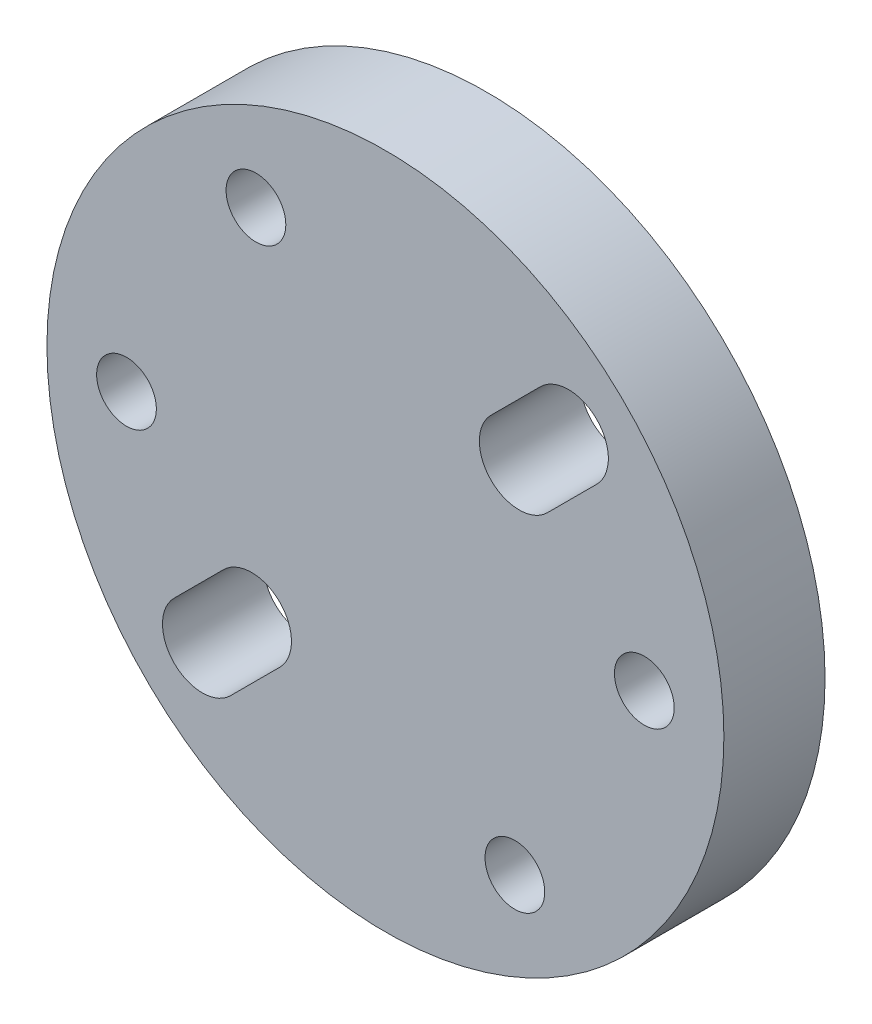
SolidWorks part; units mm, degrees
material "6061-T6 (SS)"
ref_plane "Front Plane" through (0, 0, 0) normal (0, 0, 1) x (1, 0, 0)
ref_plane "Top Plane" through (0, 0, 0) normal (0, 1, 0) x (1, 0, 0)
ref_plane "Right Plane" through (0, 0, 0) normal (1, 0, 0) x (0, 0, -1)
sketch "Sketch1" plane through (0, 0, 0) normal (0, 0, 1) x (1, 0, 0)
  circle A0 centre (0, 0) radius 16.995
  circle A1 centre (0, 0) radius 13 construction
  circle A2 centre (-13, 0) radius 1.5
  circle A3 centre (-6.5, 11.2583) radius 1.5
  circle A4 centre (6.5, 11.2583) radius 1.5
  circle A5 centre (13, 0) radius 1.5
  circle A6 centre (6.5, -11.2583) radius 1.5
  circle A7 centre (-6.5, -11.2583) radius 1.5
  dimension "D1" = 3
  dimension "D2" = 26
  dimension "D3" = 33.99
  dimension "D4" = 6
extrude "Boss-Extrude1" add sketch "Sketch1" along normal blind 5.08 contours A7 | A4 | A0 A7 A6 A5 A4 A3 A2
sketch "Sketch2" plane through (0, 0, 5.08) normal (0, 0, 1) x (1, 0, 0)
  line L0 (-9.1924, -9.1924) -> (-6.7175, -6.7175) construction
  line L3 (-10.6066, -7.7782) -> (-8.1317, -5.3033)
  line L6 (-7.7782, -10.6066) -> (-5.3033, -8.1317)
  line L7 (6.7175, 6.7175) -> (9.1924, 9.1924) construction
  line L8 (5.3033, 8.1317) -> (7.7782, 10.6066)
  line L9 (8.1317, 5.3033) -> (10.6066, 7.7782)
  line L10 (0, 0) -> (-18.2596, -18.2596) construction
  line L11 (0, 0) -> (-21.8361, 0) construction
  circle A0 centre (0, 0) radius 15
  circle A1 centre (0, 0) radius 7.5
  arc A6 (-10.6066, -7.7782) -> (-7.7782, -10.6066) centre (-9.1924, -9.1924) ccw
  arc A7 (-5.3033, -8.1317) -> (-8.1317, -5.3033) centre (-6.7175, -6.7175) ccw
  arc A8 (5.3033, 8.1317) -> (8.1317, 5.3033) centre (6.7175, 6.7175) ccw
  arc A9 (10.6066, 7.7782) -> (7.7782, 10.6066) centre (9.1924, 9.1924) ccw
  point P6 (-7.955, -7.955)
  point P11 (7.955, 7.955)
  dimension "D1" = 3.5
  dimension "D2" = 15
  dimension "D3" = 45
  dimension "D4" = 4
extrude "Cut-Extrude2" cut sketch "Sketch2" against normal blind 10 contours A7 L3 A6 L6 | A9 L8 A8 L9
